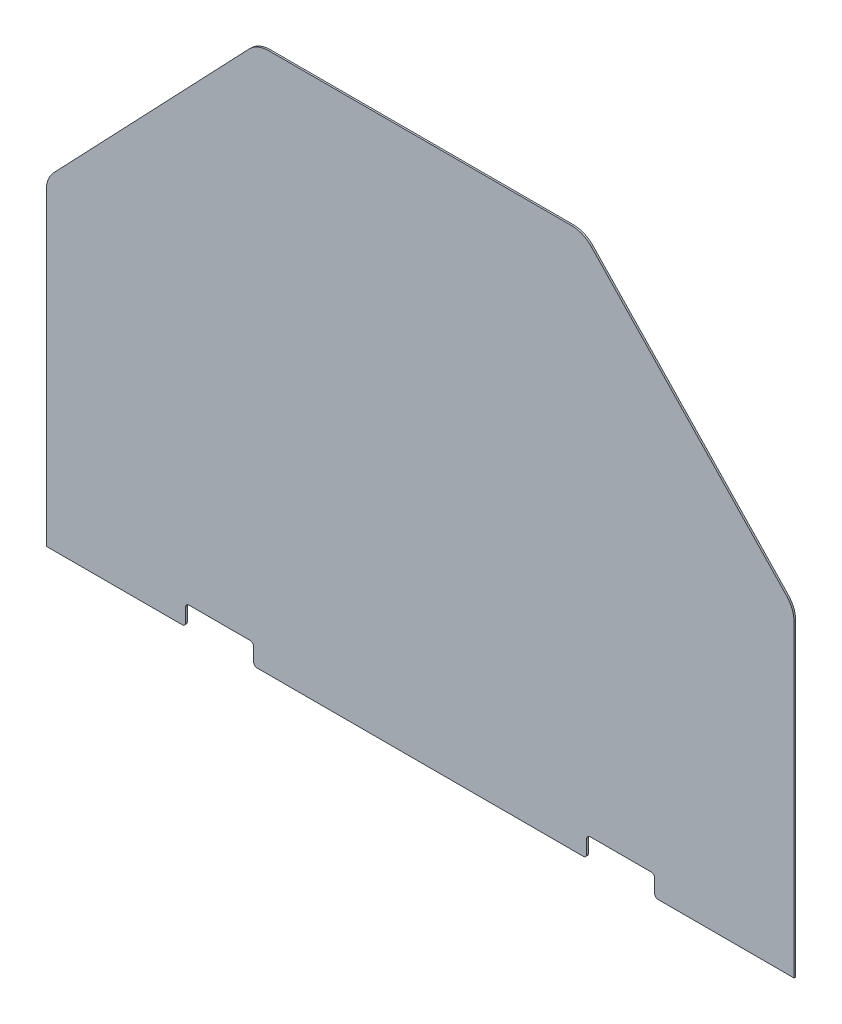
SolidWorks part; units mm, degrees
material "PE High Density"
ref_plane "Front Plane" through (0, 0, 0) normal (0, 0, 1) x (1, 0, 0)
ref_plane "Top Plane" through (0, 0, 0) normal (0, 1, 0) x (1, 0, 0)
ref_plane "Right Plane" through (0, 0, 0) normal (1, 0, 0) x (0, 0, -1)
sketch "Sketch1" plane through (0, 0, 0) normal (0, 0, 1) x (1, 0, 0)
  line L0 (-304.8, 1009.65) -> (304.8, 1009.65)
  line L1 (304.8, 1009.65) -> (698.5, 596.9)
  line L2 (698.5, 596.9) -> (698.5, 0)
  line L4 (0, 0) -> (0, 1009.65) construction
  line L7 (371.475, 0) -> (698.5, 0) construction
  line L8 (698.5, 0) -> (698.5, 127) construction
  line L9 (-698.5, 0) -> (-698.5, 127) construction
  line L10 (-371.475, 0) -> (-441.325, 0) construction
  line L16 (-698.5, 0) -> (698.5, 0)
  line L21 (-698.5, 596.9) -> (-698.5, 0)
  line L22 (-304.8, 1009.65) -> (-698.5, 596.9)
  dimension "D1" = 1009.65
  dimension "D2" = 596.9
  dimension "D3" = 698.5
  dimension "D4" = 304.8
extrude "Boss-Extrude1" add sketch "Sketch1" along normal blind 3.175
fillet "Fillet2" radius 50.8 4 edges at (698.5, 596.9, 1.5875) (304.8, 1009.65, 1.5875) (-304.8, 1009.65, 1.5875) (-698.5, 596.9, 1.5875)
sketch "Sketch2" plane through (0, 0, 0) normal (0, 0, -1) x (-1, 0, 0)
  line L0 (698.5, 576.5574) -> (698.5, 0) construction
  line L1 (311.15, 0) -> (438.15, 0)
  line L2 (311.15, 0) -> (311.15, 38.1)
  line L3 (311.15, 38.1) -> (438.15, 38.1)
  line L4 (438.15, 0) -> (438.15, 38.1)
  line L5 (698.5, 0) -> (-698.5, 0) construction
  line L6 (0, 1009.65) -> (0, 0) construction
  line L7 (-283.0517, 1009.65) -> (283.0517, 1009.65) construction
  line L8 (-438.15, 0) -> (-438.15, 38.1)
  line L9 (-311.15, 38.1) -> (-438.15, 38.1)
  line L10 (-311.15, 0) -> (-311.15, 38.1)
  line L11 (-311.15, 0) -> (-438.15, 0)
  dimension "D1" = 127
  dimension "D2" = 260.35
  dimension "D3" = 38.1
extrude "Cut-Extrude1" cut sketch "Sketch2" against normal through all
fillet "Fillet3" radius 6.35 8 edges at (-438.15, 38.1, 1.5875) (-438.15, 0, 1.5875) (-311.15, 38.1, 1.5875) (-311.15, 0, 1.5875) (311.15, 0, 1.5875) (311.15, 38.1, 1.5875) (438.15, 38.1, 1.5875) (438.15, 0, 1.5875)
